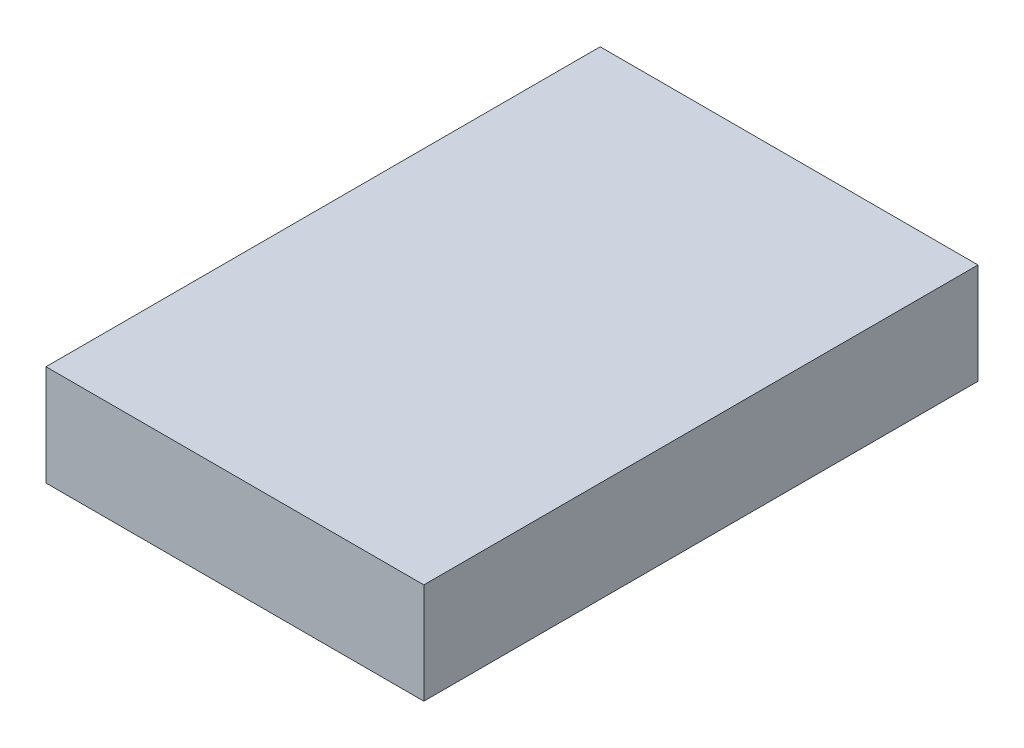
SolidWorks part; units mm, degrees
ref_plane "Front Plane" through (0, 0, 0) normal (0, 0, 1) x (1, 0, 0)
ref_plane "Top Plane" through (0, 0, 0) normal (0, 1, 0) x (1, 0, 0)
ref_plane "Right Plane" through (0, 0, 0) normal (1, 0, 0) x (0, 0, -1)
sketch "Sketch1" plane through (0, 0, 0) normal (0, 1, 0) x (1, 0, 0)
  line L1 (0, 0) -> (30, 0)
  line L2 (0, 0) -> (0, 44)
  line L3 (0, 44) -> (30, 44)
  line L4 (30, 0) -> (30, 44)
  dimension "D1" = 44
  dimension "D2" = 30
extrude "Boss-Extrude1" add sketch "Sketch1" along normal blind 8
